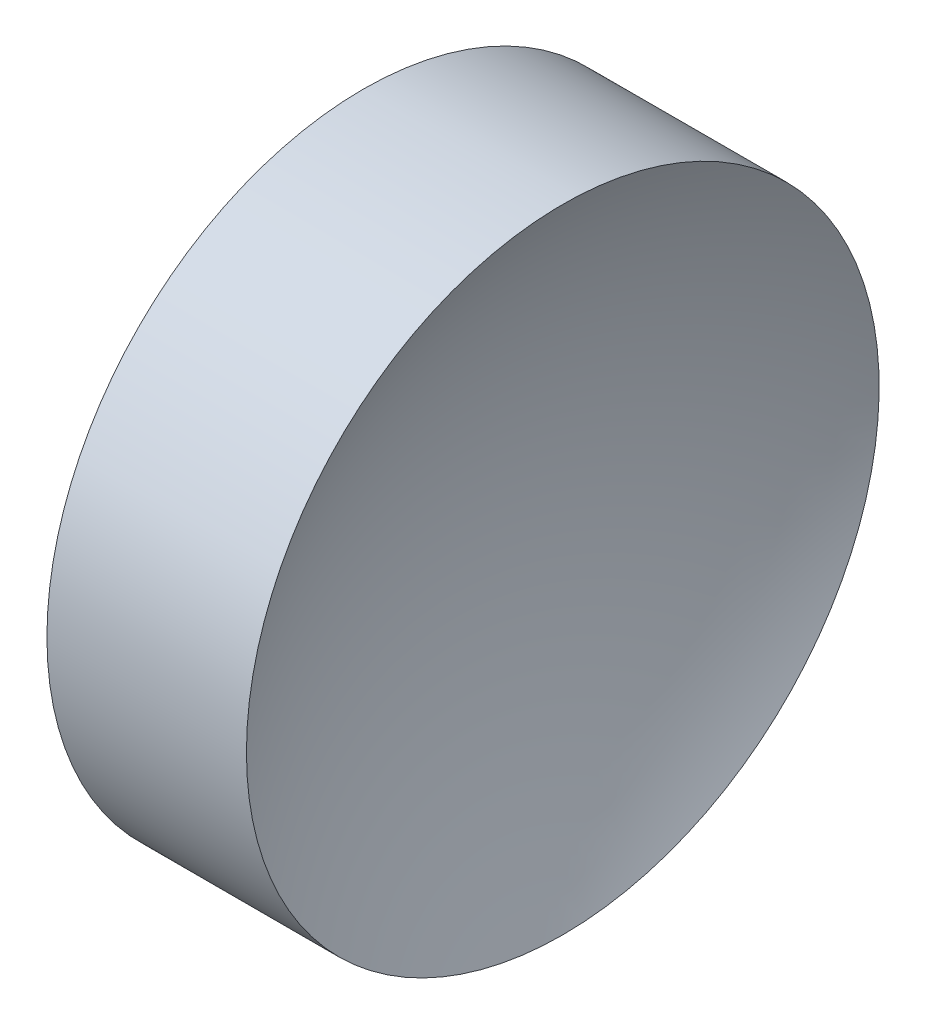
SolidWorks part; units mm, degrees
ref_plane "前视基准面" through (0, 0, 0) normal (0, 0, 1) x (1, 0, 0)
ref_plane "上视基准面" through (0, 0, 0) normal (0, 1, 0) x (1, 0, 0)
ref_plane "右视基准面" through (0, 0, 0) normal (1, 0, 0) x (0, 0, -1)
sketch "草图1" plane through (0, 0, 0) normal (0, 0, 1) x (1, 0, 0)
  line L0 (106.1247, 65.2226) -> (139.1613, 65.2226) construction
  line L1 (121.5749, 65.2226) -> (118.5749, 65.2226)
  line L3 (120.0749, 90.2226) -> (127.9578, 90.2226)
  line L4 (120.0749, 90.2226) -> (112.1919, 90.2226)
  arc A0 (127.9578, 90.2226) -> (121.5749, 65.2226) centre (173.7249, 65.2226) ccw
  arc A1 (118.5749, 65.2226) -> (112.1919, 90.2226) centre (66.4249, 65.2226) ccw
revolve "旋转1" add sketch "草图1" angle 360 about L0
